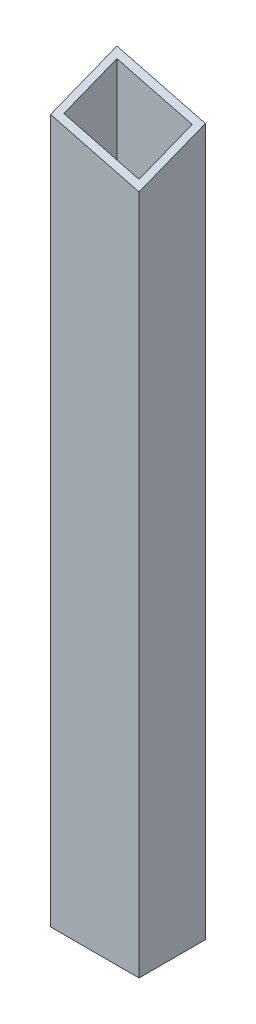
SolidWorks part; units mm, degrees
ref_plane "Vorderansicht" through (0, 0, 0) normal (0, 0, 1) x (1, 0, 0)
ref_plane "Draufsicht" through (0, 0, 0) normal (0, 1, 0) x (1, 0, 0)
ref_plane "Seitenansicht" through (0, 0, 0) normal (1, 0, 0) x (0, 0, -1)
sketch "Sketch1" plane through (0, 0, 0) normal (0, 1, 0) x (1, 0, 0)
  line L1 (20, 15) -> (-20, 15)
  line L2 (20, 15) -> (20, -15)
  line L3 (20, -15) -> (-20, -15)
  line L4 (-20, 15) -> (-20, -15)
  line L5 (20, 15) -> (-20, -15) construction
  line L6 (20, -15) -> (-20, 15) construction
  point P0 (0, 0)
  dimension "D1" = 40
  dimension "D2" = 30
extrude "Extrude-Thin1" add sketch "Sketch1" along normal blind 330 thin thin type one direction reverse wall 3
sketch "Sketch2" plane through (-20, 0, 0) normal (-1, 0, 0) x (0, 0, 1)
  line L0 (-15, 330) -> (15, 330)
  line L1 (15, 330) -> (15, 318.1827)
  line L2 (15, 330) -> (15, 0) construction
  line L3 (15, 318.1827) -> (-15, 330)
  dimension "D1" = 68.5
extrude "Extrude1" cut sketch "Sketch2" against normal through all
sketch "Sketch3" plane through (0, 0, -15) normal (0, 0, -1) x (-1, 0, 0)
  line L0 (20, 330) -> (-20, 330)
  line L1 (-20, 330) -> (-20, 319.6553)
  line L2 (-20, 330) -> (-20, 0) construction
  line L3 (-20, 319.6553) -> (20, 330)
  dimension "D1" = 75.5
extrude "Extrude2" cut sketch "Sketch3" along direction (0, -0.3665, 0.9304) on the side against the normal through all
